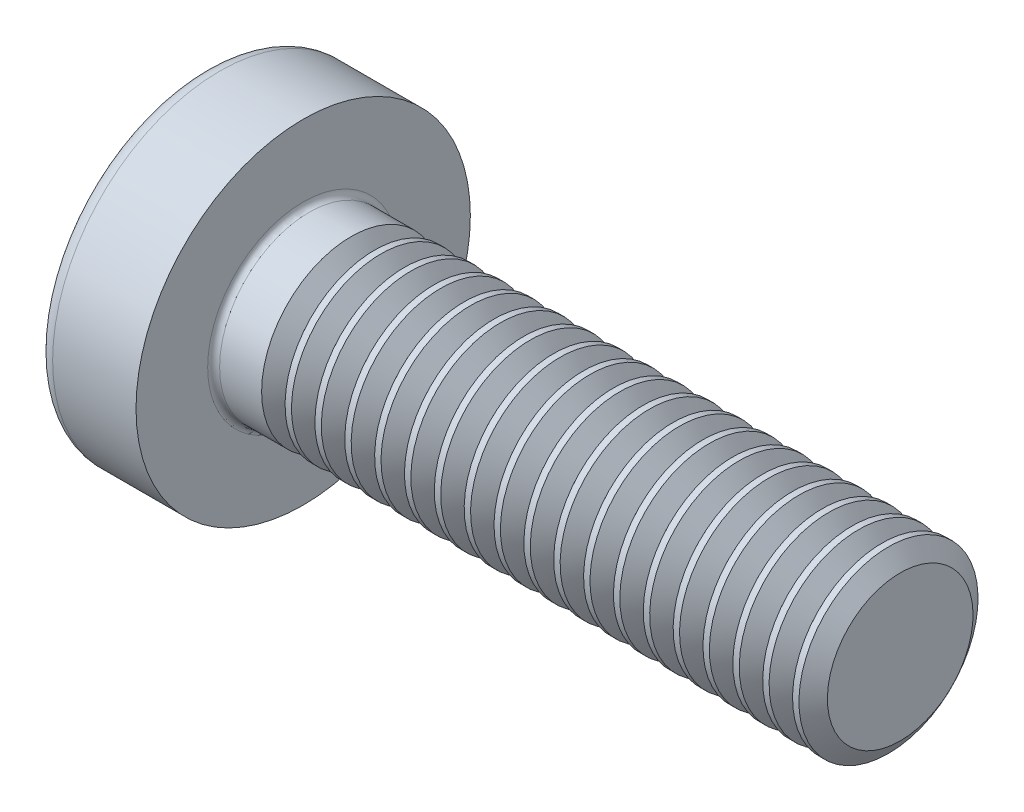
SolidWorks part; units mm, degrees
material "AISI 316 Annealed Stainless Steel Bar (SS)"
ref_plane "Plane1" through (0, 0, 0) normal (0, 0, 1) x (1, 0, 0)
ref_plane "Plane2" through (0, 0, 0) normal (0, 1, 0) x (1, 0, 0)
ref_plane "Plane3" through (0, 0, 0) normal (1, 0, 0) x (0, 0, -1)
sketch "BodySke" plane through (0, 0, 0) normal (0, 0, 1) x (1, 0, 0)
  line L0 (2.4, 1.5) -> (2.4, 2.8)
  line L1 (2.65, 6.35) -> (2.65, -3.175) construction
  line L2 (-25.4, 0) -> (127, 0) construction
  line L3 (12.4, 0) -> (0, 0)
  line L4 (2.4, 1.5) -> (12.4, 1.5)
  line L5 (12.4, 1.5) -> (12.4, 0)
  line L6 (1.0035, 2.8) -> (2.4, 2.8)
  line L8 (2.4, 6.35) -> (2.4, -3.175) construction
  arc A0 (0.7754, 2.6744) -> (0, 0) centre (5, 0) ccw
  arc A2 (0.7754, 2.6744) -> (1.0035, 2.8) centre (1.0035, 2.53) cw
  dimension "Head_crown_rad" = 5
  dimension "Head_fillet_rad" = 0.27
  dimension "Length" = 10
  dimension "Head_ht" = 2.4
  dimension "Head_dia" = 5.6
  dimension "Advance" = 0.5
  dimension "Thread_nom" = 10
  dimension "Diameter" = 3
revolve "Base-Revolve" add sketch "BodySke"
cosmetic thread "ThreadCosmetic" [suppressed]
fillet "Fillet1" radius 0.1 1 edges at (2.4, 0, 1.5)
sketch "Sketch3" plane through (0, 0, 0) normal (1, 0, 0) x (0, 0, -1)
  line L0 (0.37, -1.4) -> (-0.37, -1.4)
  line L1 (0.37, -1.4) -> (0.37, 1.4)
  line L2 (-0.37, 1.4) -> (0.37, 1.4)
  line L3 (-0.37, 1.4) -> (-0.37, -1.4)
  dimension "Cross_dia" = 2.8
  dimension "D1" = 1.4
  dimension "Cross_width" = 0.74
  dimension "D2" = 0.37
ref_plane "Plane4" through (1.75, 0, 0) normal (1, 0, 0) x (0, 0, -1)
sketch "Sketch4" plane through (1.75, 0, 0) normal (1, 0, 0) x (0, 0, -1)
  line L0 (0.37, -0.5275) -> (-0.37, -0.5275)
  line L1 (0.37, -0.5275) -> (0.37, 0.5275)
  line L2 (-0.37, 0.5275) -> (0.37, 0.5275)
  line L3 (-0.37, 0.5275) -> (-0.37, -0.5275)
  dimension "D1" = 0.74
  dimension "D2" = 1.055
  dimension "D3" = 0.37
  dimension "D4" = 0.5275
loft "Recess" cut profiles "Sketch3", "Sketch4"
pattern_circular "RecPat" count 2 every 90 about axis through (0, 0, 0) along (1, 0, 0) of "Recess"
sketch "RecCorSke" plane through (0, 0, 0) normal (0, 0, 1) x (1, 0, 0)
  line L0 (-3.175, 0) -> (15.875, 0) construction
  line L1 (-25.4, 0) -> (127, 0) construction
  line L2 (0, 0) -> (0, 0.6784)
  line L3 (0, 0.6784) -> (1.75, 0.556)
  line L4 (1.75, 0.556) -> (1.9307, 0)
  line L5 (1.9307, 0) -> (0, 0)
  dimension "Diameter" = 1.112
  dimension "Depth" = 1.75
  dimension "Draft_angle" = 4
  dimension "Bottom_angle" = 18
revolve "RecessCore" cut sketch "RecCorSke" angle 360 about L0
sketch "ThdSchSke" plane through (0, 0, 0) normal (0, 0, 1) x (1, 0, 0)
  line L0 (3.4, -1.2195) -> (3.2036, -1.5)
  line L1 (3.4, -1.2195) -> (3.5964, -1.5)
  line L2 (3.5964, -1.5) -> (3.5964, -1.875)
  line L3 (-3.175, 0) -> (5.1513, 0) construction
  line L5 (3.5964, -1.875) -> (3.2036, -1.875)
  line L6 (3.2036, -1.875) -> (3.2036, -1.5)
  dimension "Diameter" = 3
  dimension "SideAngle" = 55
  dimension "VeeAngle" = 70
  dimension "Thread_minor" = 2.439
  dimension "Overcut" = 3.75
  dimension "Start" = 3.4
revolve "ThreadSchematic" cut sketch "ThdSchSke" angle 360 about L3
pattern_linear "ThdSchPat" count 19 spacing 0.5 along (1, 0, 0) of "ThreadSchematic"
equation "\"D1@Sketch3\" = \"Cross_dia@Sketch3\" / 2"
equation "\"D2@Sketch3\" = \"Cross_width@Sketch3\" / 2"
equation "\"Depth@RecCorSke\" = \"Cross_depth@Plane4\""
equation "\"D1@Sketch4\" = \"Cross_width@Sketch3\""
equation "\"D2@Sketch4\" = \"Cross_dia@Sketch3\" - 2.0 * \"Cross_depth@Plane4\" * tan(26.5  * 0.017453292)"
equation "\"D3@Sketch4\" = \"D1@Sketch4\" / 2"
equation "\"D4@Sketch4\" = \"D2@Sketch4\" / 2"
equation "\"Thread_length@ThreadCosmetic\" = ((sgn( (\"Length@BodySke\" - \"Advance@BodySke\" * 2.0 ) - \"Thread_nom@BodySke\" )-1)*( (\"Length@BodySke\" - \"Advance@BodySke\" * 2.0 ) - \"Thread_nom@BodySke\" ))/-2+ \"Thread_nom@BodySke\""
equation "\"Thread_minor@ThdSchSke\" = \"Thread_minor@ThreadCosmetic\""
equation "\"Diameter@ThdSchSke\" = \"Diameter@BodySke\""
equation "\"Overcut@ThdSchSke\" = \"Diameter@BodySke\" * 1.25"
equation "\"Start@ThdSchSke\" = \"Head_ht@BodySke\" + \"Length@BodySke\" - \"Thread_length@ThreadCosmetic\"  '---Non-countersunk---"
equation "\"Num_threads@ThdSchPat\" = int( \"Thread_length@ThreadCosmetic\" / \"Advance@BodySke\" + 0.999 )  + 1"
equation "\"Advance@ThdSchPat\" = \"Thread_length@ThreadCosmetic\" /  (\"Num_threads@ThdSchPat\" - 1) 'relax it"
